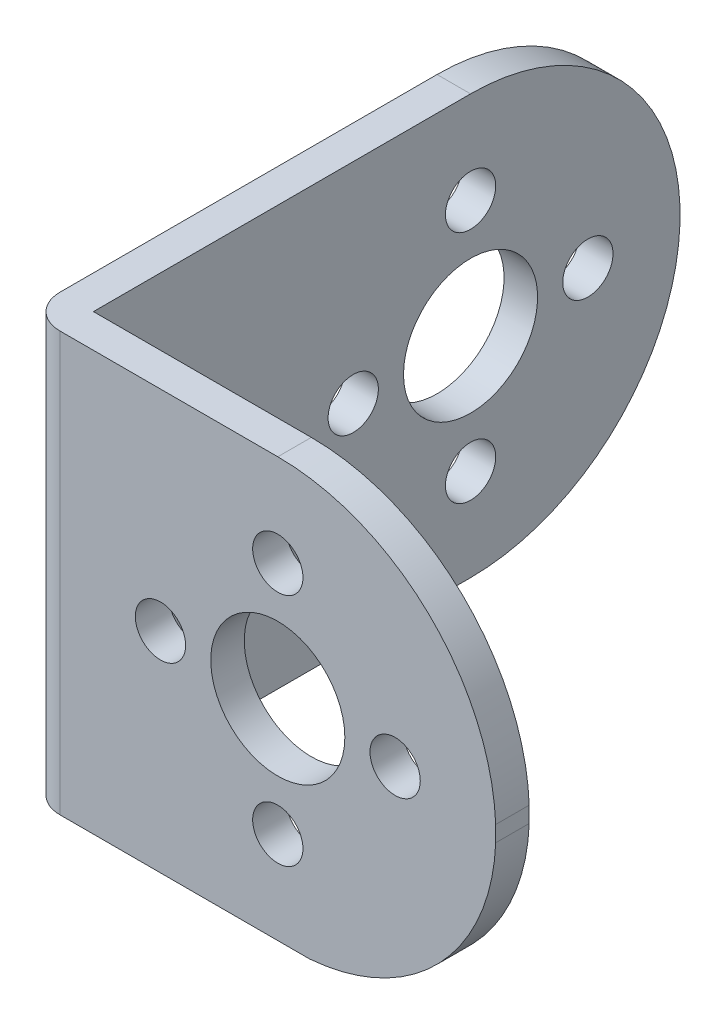
SolidWorks part; units mm, degrees
ref_plane "Piano frontale" through (0, 0, 0) normal (0, 0, 1) x (1, 0, 0)
ref_plane "Piano superiore" through (0, 0, 0) normal (0, 1, 0) x (1, 0, 0)
ref_plane "Piano destro" through (0, 0, 0) normal (1, 0, 0) x (0, 0, -1)
sketch "Schizzo1" plane through (0, 0, 0) normal (0, 1, 0) x (1, 0, 0)
  line L0 (11.0355, -4.4811) -> (-16.9645, -4.4811)
  line L1 (-16.9645, -4.4811) -> (-16.9645, 32.5189)
  line L2 (-16.9645, 32.5189) -> (-14.9645, 32.5189)
  line L3 (-14.9645, 32.5189) -> (-14.9645, -2.4811)
  line L4 (-14.9645, -2.4811) -> (11.0355, -2.4811)
  line L5 (11.0355, -2.4811) -> (11.0355, -4.4811)
  dimension "D1" = 28
  dimension "D2" = 37
  dimension "D3" = 2
  dimension "D4" = 2
extrude "Estrusione-Estrusione1" add sketch "Schizzo1" along normal blind 25
fillet "Raccordo1" radius 2 1 edges at (-16.9645, 12.5, 4.4811)
sketch "Schizzo2" plane through (-16.9645, 0, 0) normal (-1, 0, 0) x (0, 0, 1)
  line L0 (-32.5189, 12.5) -> (2.4811, 12.5) construction
  line L1 (-32.5189, 25) -> (-32.5189, 0) construction
  line L2 (2.4811, 0) -> (2.4811, 25) construction
  line L3 (2.4811, 12.5) -> (-15.0189, 12.5) construction
  line L4 (-15.0189, 12.5) -> (-15.0189, 25) construction
  line L5 (-32.5189, 25) -> (2.4811, 25) construction
  line L6 (-15.0189, 25) -> (-15.0189, 0) construction
  line L7 (-32.5189, 0) -> (2.4811, 0) construction
  line L8 (-32.5189, 25) -> (-32.5189, 0)
  circle A0 centre (-20.0189, 12.5) radius 12.5
  point P15 (-20.0189, 25)
  point P16 (-20.0189, 0)
  point P17 (-32.5189, 12.5)
  line M2 (-32.5189, 0) -> (2.4811, 0)
  line M4 (2.4811, 25) -> (-32.5189, 25)
  line M5 (-32.5189, 25) -> (-32.5189, 0)
extrude "Taglio-Estrusione1" cut sketch "Schizzo2" against normal through all contours A0 L8 M2 | A0 M4 M5
sketch "Schizzo4" plane through (0, 0, 4.4811) normal (0, 0, 1) x (1, 0, 0)
  line L0 (-1.9645, 25) -> (-1.9645, 0) construction
  line L1 (-14.9645, 25) -> (11.0355, 25) construction
  line L2 (-14.9645, 0) -> (11.0355, 0) construction
  line L3 (-1.9645, 0) -> (11.0355, 12.5) construction
  line L4 (11.0355, 25) -> (11.0355, 0) construction
  line L5 (11.0355, 12.5) -> (-1.9645, 25) construction
  line L6 (11.0355, 12.5) -> (-14.9645, 12.5) construction
  line L7 (-14.9645, 25) -> (-14.9645, 0) construction
  arc A1 (-1.9645, 25) -> (11.0355, 12.5) centre (10.5451, 25) ccw
  arc A2 (11.0355, 12.5) -> (-1.9645, 25) centre (-1.9645, 11.99) ccw
  arc A3 (11.0355, 12.5) -> (-1.9645, 0) centre (11.5676, -1.0634) ccw
  arc A4 (11.0355, 12.5) -> (-1.9645, 0) centre (-1.0194, 12.0271) cw
  point P17 (-1.9645, 25)
  point P18 (11.0355, 12.5)
  point P19 (-1.9645, 0)
extrude "Taglio-Estrusione3" cut sketch "Schizzo4" against normal through all contours A2 L4 L1 | L4 A4 L3
sketch "Schizzo6" plane through (0, 0, 4.4811) normal (0, 0, 1) x (1, 0, 0)
  line L0 (-14.9645, 12.5) -> (11.0355, 12.5) construction
  line L1 (-14.9645, 25) -> (-14.9645, 0) construction
  line L2 (11.0355, 12.5) -> (-1.9645, 12.5) construction
  line L3 (-1.9645, 12.5) -> (-1.9645, 25) construction
  line L4 (-1.9645, 25) -> (-1.9645, 0) construction
  line L5 (-14.9645, 0) -> (-0.0742, 0) construction
  circle A0 centre (-1.9645, 12.5) radius 4
  circle A1 centre (-1.9645, 19.5) radius 1.5
  circle A2 centre (-1.9645, 5.5) radius 1.5
  circle A3 centre (5.0355, 12.5) radius 1.5
  circle A4 centre (-8.9645, 12.5) radius 1.5
  dimension "D1" = 3
  dimension "D2" = 3
  dimension "D3" = 3
  dimension "D4" = 3
  dimension "D5" = 8
  dimension "D6" = 7
  dimension "D7" = 7
  dimension "D8" = 7
  dimension "D9" = 7
extrude "Taglio-Estrusione4" cut sketch "Schizzo6" against normal through all
sketch "Schizzo7" plane through (-16.9645, 0, 0) normal (-1, 0, 0) x (0, 0, 1)
  line L0 (2.4811, 12.5) -> (-32.5189, 12.5) construction
  line L1 (2.4811, 0) -> (2.4811, 25) construction
  line L2 (-32.5189, 12.5) -> (-15.0189, 12.5) construction
  line L3 (-15.0189, 12.5) -> (-15.0189, 25) construction
  line L4 (-20.0189, 25) -> (2.4811, 25) construction
  line L5 (-15.0189, 25) -> (-15.0189, 0) construction
  line L6 (-20.0189, 0) -> (2.4811, 0) construction
  line L7 (-20.0189, 25) -> (-20.0189, 0) construction
  arc A0 (-20.0189, 25) -> (-20.0189, 0) centre (-20.0189, 12.5) ccw construction
  circle A1 centre (-20.0189, 12.5) radius 4
  circle A2 centre (-27.0189, 12.5) radius 1.5
  circle A3 centre (-20.0189, 19.5) radius 1.5
  circle A4 centre (-20.0189, 5.5) radius 1.5
  circle A5 centre (-13.0189, 12.5) radius 1.5
  dimension "D1" = 8
  dimension "D2" = 3
  dimension "D3" = 3
  dimension "D4" = 3
  dimension "D5" = 3
  dimension "D6" = 7
  dimension "D7" = 7
  dimension "D8" = 7
  dimension "D9" = 7
extrude "Taglio-Estrusione5" cut sketch "Schizzo7" against normal through all
